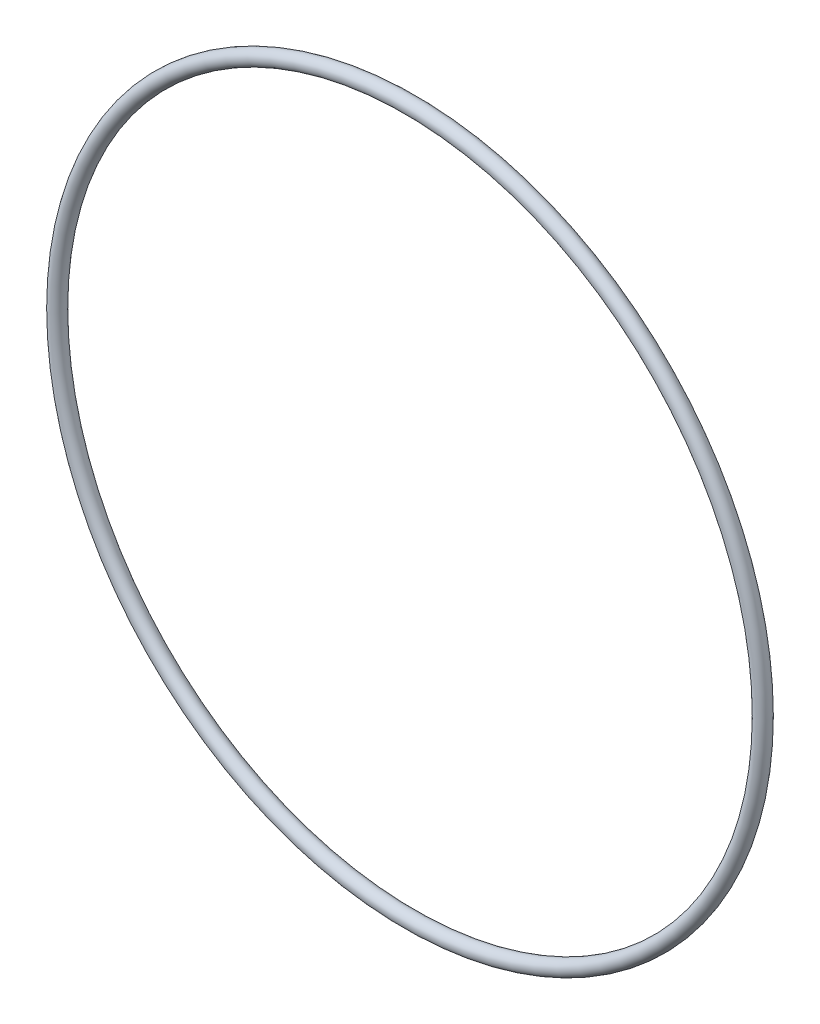
SolidWorks part; units mm, degrees
ref_plane "Front" through (0, 0, 0) normal (0, 0, 1) x (1, 0, 0)
ref_plane "Top" through (0, 0, 0) normal (0, 1, 0) x (1, 0, 0)
ref_plane "Right" through (0, 0, 0) normal (1, 0, 0) x (0, 0, -1)
sketch "Sketch1" plane through (0, 0, 0) normal (1, 0, 0) x (0, -1, 0)
  line L0 (0, -0.889) -> (0, 0.889) construction
  line L2 (-47.2046, 0) -> (47.2046, 0) construction
  line L3 (-41.1353, 0) -> (41.1353, 0) construction
  circle A0 centre (42.0243, 0) radius 0.889
  point P9 (41.1353, 0)
  point P10 (42.9133, 0)
  point P13 (42.0243, 0.889)
  point P14 (42.0243, -0.889)
  dimension "Width" = 1.778
  dimension "ID" = 82.2706
revolve "Revolve1" add sketch "Sketch1" angle 360 about L0
